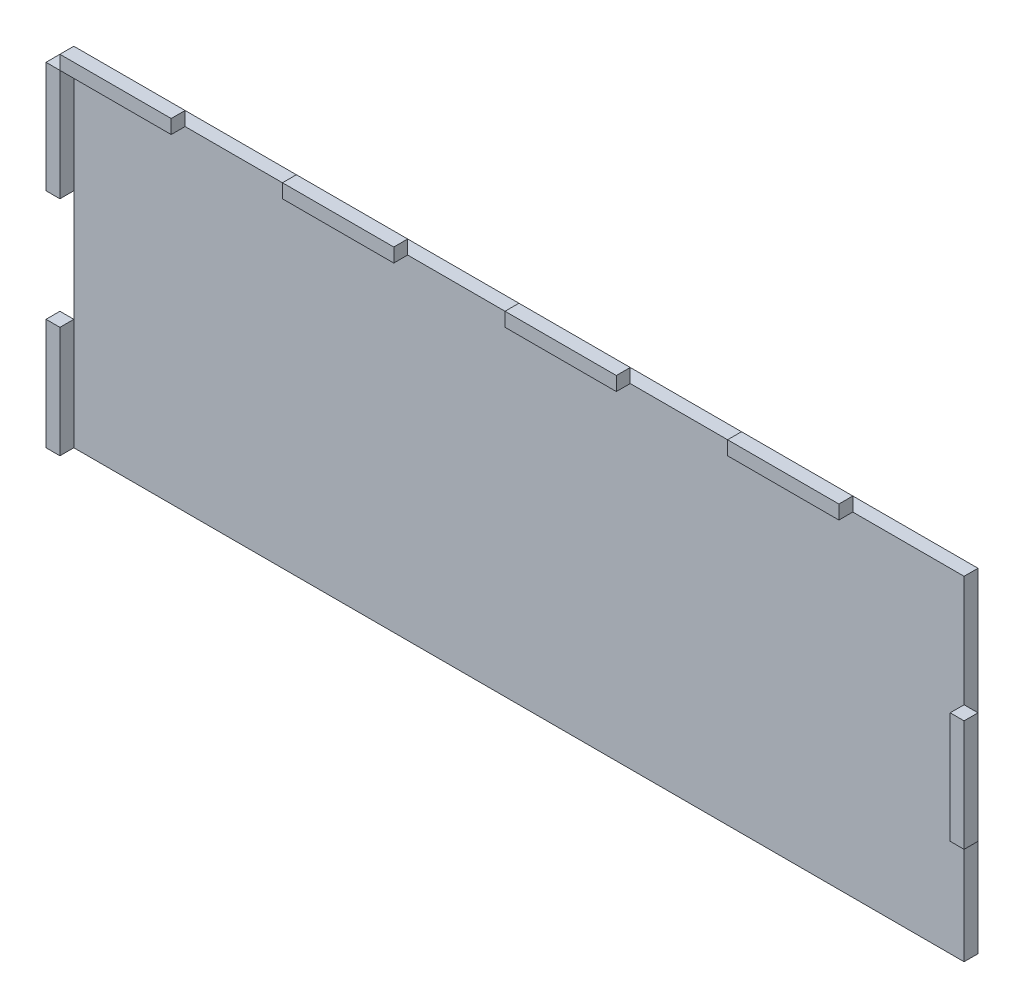
SolidWorks part; units mm, degrees
ref_plane "Front Plane" through (0, 0, 0) normal (0, 0, 1) x (1, 0, 0)
ref_plane "Top Plane" through (0, 0, 0) normal (0, 1, 0) x (1, 0, 0)
ref_plane "Right Plane" through (0, 0, 0) normal (1, 0, 0) x (0, 0, -1)
sketch "Sketch1" plane through (0, 0, 0) normal (0, 0, 1) x (1, 0, 0)
  line L1 (-101.6, -38.1) -> (101.6, -38.1)
  line L2 (-101.6, -38.1) -> (-101.6, 38.1)
  line L3 (-101.6, 38.1) -> (101.6, 38.1)
  line L4 (101.6, -38.1) -> (101.6, 38.1)
  line L5 (-101.6, -38.1) -> (101.6, 38.1) construction
  line L6 (-101.6, 38.1) -> (101.6, -38.1) construction
  point P0 (0, 0)
  dimension "D1" = 203.2
  dimension "D2" = 76.2
extrude "Boss-Extrude1" add sketch "Sketch1" along normal blind 3.175
sketch "Sketch2" plane through (0, 0, 3.175) normal (0, 0, 1) x (1, 0, 0)
  line L0 (-50.8, 38.1) -> (-50.8, 41.275)
  line L1 (-101.6, 38.1) -> (-76.2, 38.1)
  line L2 (-101.6, 38.1) -> (-101.6, 41.275)
  line L3 (-101.6, 41.275) -> (-76.2, 41.275)
  line L4 (-76.2, 38.1) -> (-76.2, 41.275)
  line L5 (-50.8, 38.1) -> (-25.4, 38.1)
  line L6 (-25.4, 38.1) -> (-25.4, 41.275)
  line L7 (-50.8, 41.275) -> (-25.4, 41.275)
  line L8 (0, 38.1) -> (0, 41.275)
  line L9 (0, 38.1) -> (25.4, 38.1)
  line L10 (25.4, 38.1) -> (25.4, 41.275)
  line L11 (0, 41.275) -> (25.4, 41.275)
  line L12 (50.8, 38.1) -> (50.8, 41.275)
  line L13 (50.8, 38.1) -> (76.2, 38.1)
  line L14 (76.2, 38.1) -> (76.2, 41.275)
  line L15 (50.8, 41.275) -> (76.2, 41.275)
  point P5 (-76.2, 39.6875)
  dimension "D1" = 25.4
  dimension "D2" = 3.175
  dimension "D3" = 4
extrude "Boss-Extrude2" add sketch "Sketch2" along normal blind 3.175 separate body
sketch "Sketch4" plane through (0, 0, 3.175) normal (0, 0, 1) x (1, 0, 0)
  line L1 (-101.6, -38.1) -> (-104.775, -38.1)
  line L2 (-101.6, -38.1) -> (-101.6, -12.7)
  line L3 (-101.6, -12.7) -> (-104.775, -12.7)
  line L4 (-104.775, -38.1) -> (-104.775, -12.7)
  line L5 (-101.6, 38.1) -> (-104.775, 38.1)
  line L6 (-101.6, 38.1) -> (-101.6, 12.7)
  line L7 (-101.6, 12.7) -> (-104.775, 12.7)
  line L8 (-104.775, 38.1) -> (-104.775, 12.7)
  dimension "D1" = 25.4
  dimension "D2" = 3.175
  dimension "D3" = 25.4
extrude "Boss-Extrude4" add sketch "Sketch4" along normal blind 3.175 separate body
sketch "Sketch6" plane through (0, 0, 3.175) normal (0, 0, 1) x (1, 0, 0)
  line L0 (101.6, -38.1) -> (101.6, 38.1) construction
  line L1 (101.6, 12.7) -> (104.775, 12.7)
  line L2 (101.6, 12.7) -> (101.6, -12.7)
  line L3 (101.6, -12.7) -> (104.775, -12.7)
  line L4 (104.775, 12.7) -> (104.775, -12.7)
  line L5 (101.6, 38.1) -> (-101.6, 38.1) construction
  dimension "D1" = 25.4
  dimension "D2" = 25.4
  dimension "D3" = 3.175
extrude "Boss-Extrude6" add sketch "Sketch6" along normal blind 3.175 separate body
